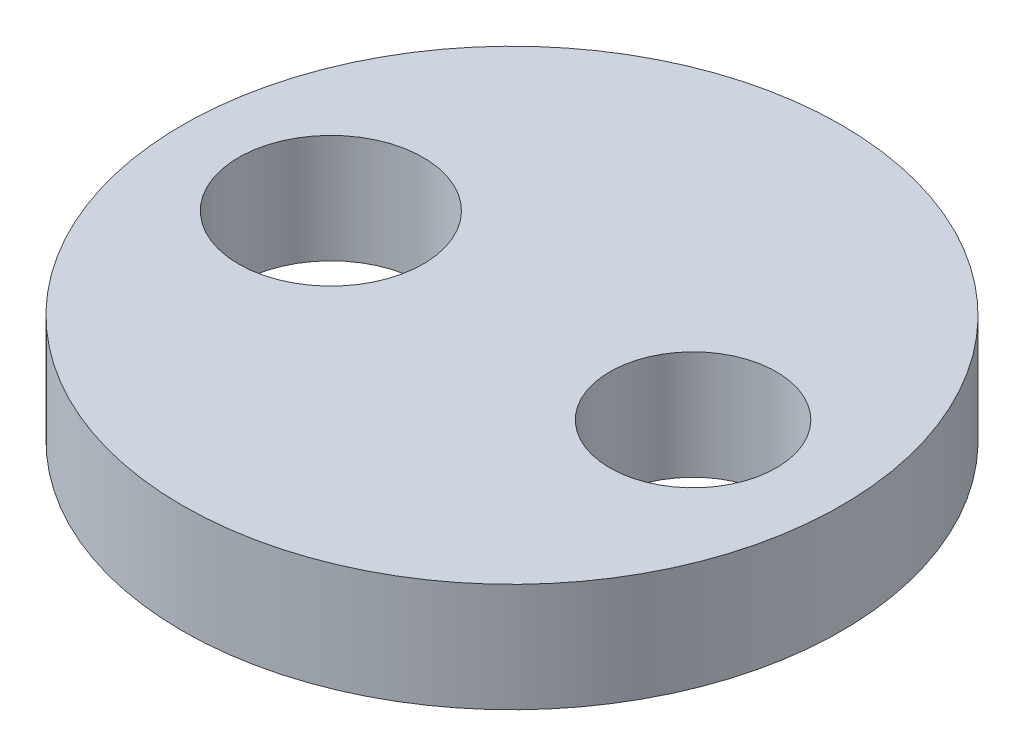
SolidWorks part; units mm, degrees
ref_plane "Front Plane" through (0, 0, 0) normal (0, 0, 1) x (1, 0, 0)
ref_plane "Top Plane" through (0, 0, 0) normal (0, 1, 0) x (1, 0, 0)
ref_plane "Right Plane" through (0, 0, 0) normal (1, 0, 0) x (0, 0, -1)
sketch "Sketch1" plane through (0, 0, 0) normal (0, 1, 0) x (1, 0, 0)
  circle A0 centre (0, 0) radius 9.1
  circle A1 centre (5, 0) radius 2.3
  circle A2 centre (-5, -0.0008) radius 2.55
  dimension "D1" = 18.2
  dimension "D4" = 5.1
  dimension "D5" = 4.6
  dimension "D2" = 5
  dimension "D3" = 5
extrude "Boss-Extrude1" add sketch "Sketch1" along normal blind 3
